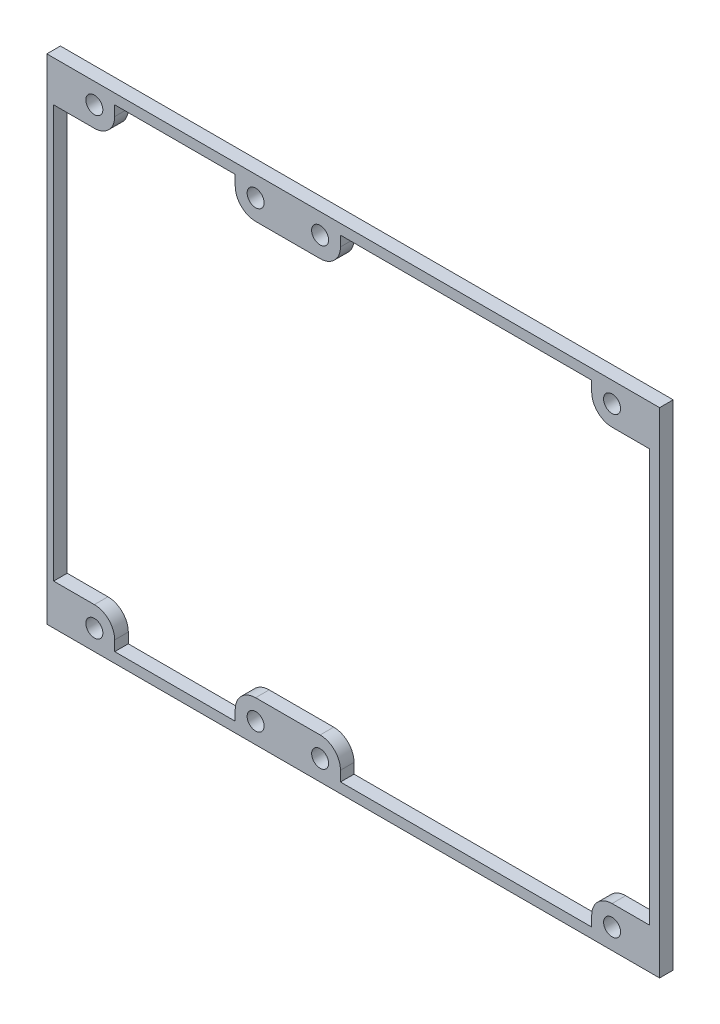
SolidWorks part; units mm, degrees
ref_plane "Front Plane" through (0, 0, 0) normal (0, 0, 1) x (1, 0, 0)
ref_plane "Top Plane" through (0, 0, 0) normal (0, 1, 0) x (1, 0, 0)
ref_plane "Right Plane" through (0, 0, 0) normal (1, 0, 0) x (0, 0, -1)
sketch "Sketch2" plane through (0, 0, 0) normal (0, 0, 1) x (1, 0, 0)
  line L1 (-90.25, 72.75) -> (90.25, 72.75)
  line L2 (-90.25, 72.75) -> (-90.25, -72.75)
  line L3 (-90.25, -72.75) -> (90.25, -72.75)
  line L4 (90.25, 72.75) -> (90.25, -72.75)
  line L5 (-90.25, 72.75) -> (90.25, -72.75) construction
  line L6 (-90.25, -72.75) -> (90.25, 72.75) construction
  point P0 (0, 0)
  dimension "D1" = 180.5
  dimension "D2" = 145.5
extrude "Boss-Extrude1" add sketch "Sketch2" along normal blind 4
sketch "Sketch5" plane through (0, 0, 4) normal (0, 0, 1) x (1, 0, 0)
  line L0 (-90.25, 72.75) -> (-90.25, -72.75) construction
  line L1 (-70.25, 69.75) -> (-34.75, 69.75)
  line L2 (-88.25, 60.75) -> (-88.25, -60.75)
  line L3 (-70.25, -69.75) -> (-34.75, -69.75)
  line L4 (87.25, 60.75) -> (87.25, -60.75)
  line L7 (-90.25, -72.75) -> (90.25, -72.75) construction
  line L8 (-88.25, 60.75) -> (-76.25, 60.75)
  line L9 (-88.25, 66.75) -> (87.25, 66.75) construction
  line L10 (-70.25, 66.75) -> (-70.25, 69.75)
  line L11 (90.25, 72.75) -> (-90.25, 72.75) construction
  line L12 (-28.75, 60.75) -> (-9.75, 60.75)
  line L13 (76.25, 60.75) -> (87.25, 60.75)
  line L14 (90.25, -72.75) -> (90.25, 72.75) construction
  line L15 (-34.75, 66.75) -> (-34.75, 69.75)
  line L16 (-3.75, 66.75) -> (-3.75, 69.75)
  line L17 (70.25, 66.75) -> (70.25, 69.75)
  line L18 (-88.25, 0) -> (88.25, 0) construction
  line L19 (-70.25, -66.75) -> (-70.25, -69.75)
  line L20 (-88.25, -60.75) -> (-76.25, -60.75)
  line L21 (-3.75, -66.75) -> (-3.75, -69.75)
  line L22 (-28.75, -60.75) -> (-9.75, -60.75)
  line L23 (-34.75, -66.75) -> (-34.75, -69.75)
  line L24 (76.25, -60.75) -> (87.25, -60.75)
  line L25 (70.25, -66.75) -> (70.25, -69.75)
  line L26 (-3.75, 69.75) -> (70.25, 69.75)
  line L27 (-3.75, -69.75) -> (70.25, -69.75)
  arc A0 (-76.25, 60.75) -> (-70.25, 66.75) centre (-76.25, 66.75) ccw
  arc A1 (-28.75, 60.75) -> (-34.75, 66.75) centre (-28.75, 66.75) cw
  arc A2 (-9.75, 60.75) -> (-3.75, 66.75) centre (-9.75, 66.75) ccw
  arc A3 (76.25, 60.75) -> (70.25, 66.75) centre (76.25, 66.75) cw
  arc A4 (-76.25, -60.75) -> (-70.25, -66.75) centre (-76.25, -66.75) cw
  arc A5 (-9.75, -60.75) -> (-3.75, -66.75) centre (-9.75, -66.75) cw
  arc A6 (-28.75, -60.75) -> (-34.75, -66.75) centre (-28.75, -66.75) ccw
  arc A7 (76.25, -60.75) -> (70.25, -66.75) centre (76.25, -66.75) ccw
  circle A8 centre (-76.25, 66.75) radius 2.5
  circle A9 centre (-28.75, 66.75) radius 2.5
  circle A10 centre (-9.75, 66.75) radius 2.5
  circle A11 centre (76.25, 66.75) radius 2.5
  circle A12 centre (76.25, -66.75) radius 2.5
  circle A13 centre (-9.75, -66.75) radius 2.5
  circle A14 centre (-28.75, -66.75) radius 2.5
  circle A15 centre (-76.25, -66.75) radius 2.5
  point P0 (0, 0)
  point P27 (-72.0074, 62.5074)
  point P41 (-72.0074, -62.5074)
  point P43 (-32.9926, 62.5074)
  point P51 (-32.9926, -62.5074)
  dimension "D10" = 5
  dimension "D11" = 5
  dimension "D12" = 5
  dimension "D13" = 5
  dimension "D1" = 2
  dimension "D2" = 3
  dimension "D3" = 3
  dimension "D4" = 14
  dimension "D5" = 12
  dimension "D6" = 61.5
  dimension "D7" = 80.5
  dimension "D8" = 14
  dimension "D9" = 3
extrude "Cut-Extrude2" cut sketch "Sketch5" against normal up to next
equation "\"D11@Sketch5\"=\"D10@Sketch5\""
equation "\"D12@Sketch5\"=\"D10@Sketch5\""
equation "\"D13@Sketch5\"=\"D10@Sketch5\""
